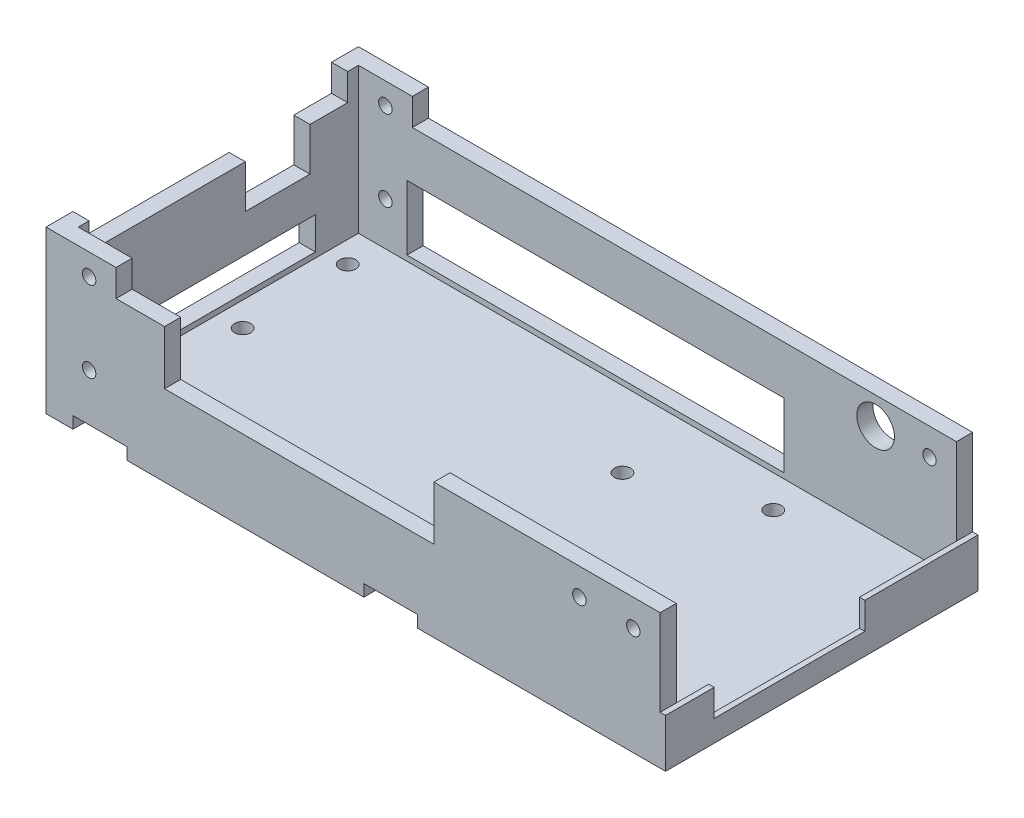
SolidWorks part; units mm, degrees
ref_plane "Front Plane" through (0, 0, 0) normal (0, 0, 1) x (1, 0, 0)
ref_plane "Top Plane" through (0, 0, 0) normal (0, 1, 0) x (1, 0, 0)
ref_plane "Right Plane" through (0, 0, 0) normal (1, 0, 0) x (0, 0, -1)
sketch "Sketch2" plane through (0, 0, 0) normal (0, 1, 0) x (1, 0, 0)
  line L1 (-76.4862, 30.6019) -> (37.5138, 30.6019)
  line L2 (-76.4862, 30.6019) -> (-76.4862, -27.3981)
  line L3 (-76.4862, -27.3981) -> (37.5138, -27.3981)
  line L4 (37.5138, 30.6019) -> (37.5138, -27.3981)
  dimension "D1" = 58
  dimension "D2" = 114
extrude "Boss-Extrude1" add sketch "Sketch2" along normal blind 3
sketch "Sketch3" plane through (0, 3, 0) normal (0, 1, 0) x (1, 0, 0)
  line L1 (37.5138, 30.6019) -> (-76.4862, 30.6019) construction
  line L2 (-76.4862, 30.6019) -> (-76.4862, -27.3981) construction
  circle A0 centre (-10.4862, 13.6019) radius 1.5
  circle A1 centre (-10.4862, -10.3981) radius 1.5
  circle A2 centre (-68.9862, 1.6019) radius 1.5
  dimension "D1" = 3
  dimension "D2" = 3
  dimension "D3" = 3
  dimension "D4" = 66
  dimension "D5" = 24
  dimension "D6" = 66
  dimension "D7" = 17
  dimension "D8" = 58.5
  dimension "D9" = 29
extrude "Cut-Extrude5" cut sketch "Sketch3" against normal through all
sketch "Sketch5" plane through (0, 0, 0) normal (0, -1, 0) x (-1, 0, 0)
  line L0 (-37.5138, 30.6019) -> (76.4862, 30.6019) construction
  circle A0 centre (23.4862, 16.8519) radius 3.025
  circle A2 centre (23.4862, -13.6481) radius 3.025
  circle A3 centre (53.9862, -13.6481) radius 3.025
  circle A4 centre (53.9862, 16.8519) radius 3.025
  circle A6 centre (10.4862, -10.3981) radius 1.5 construction
  circle A7 centre (10.4862, 13.6019) radius 1.5 construction
  dimension "D1" = 6.05
  dimension "D2" = 6.05
  dimension "D3" = 6.05
  dimension "D4" = 6.05
  dimension "D7" = 13
  dimension "D5" = 30.5
  dimension "D6" = 13.75
  dimension "D8" = 13
  dimension "D9" = 30.5
  dimension "D10" = 30.5
  dimension "D11" = 30.5
  dimension "D12" = 13.75
extrude "Cut-Extrude7" cut sketch "Sketch5" against normal blind 2.5
sketch "Sketch7" plane through (0, 3, 0) normal (0, 1, 0) x (1, 0, 0)
  line L0 (37.5138, 30.6019) -> (-76.4862, 30.6019) construction
  line L1 (-76.4862, 30.6019) -> (37.5138, 30.6019)
  line L2 (-76.4862, 30.6019) -> (-76.4862, 27.6019)
  line L3 (-76.4862, 27.6019) -> (37.5138, 27.6019)
  line L4 (37.5138, 30.6019) -> (37.5138, 27.6019)
  line L5 (-76.4862, -24.3981) -> (37.5138, -24.3981)
  line L6 (-76.4862, -24.3981) -> (-76.4862, -27.3981)
  line L7 (-76.4862, -27.3981) -> (37.5138, -27.3981)
  line L8 (37.5138, -24.3981) -> (37.5138, -27.3981)
  line L9 (-76.4862, 30.6019) -> (-76.4862, -27.3981) construction
  line L10 (-76.4862, 30.6019) -> (-76.4862, -27.3981) construction
  line L11 (-76.4862, -27.3981) -> (37.5138, -27.3981) construction
  line L12 (37.5138, -27.3981) -> (37.5138, 30.6019) construction
  line L14 (-76.4862, 27.6019) -> (-73.4862, 27.6019)
  line L15 (-76.4862, 27.6019) -> (-76.4862, -24.3981)
  line L16 (-76.4862, -24.3981) -> (-73.4862, -24.3981)
  line L17 (-73.4862, 27.6019) -> (-73.4862, -24.3981)
  point P16 (37.5138, 29.1019)
  dimension "D1" = 3
  dimension "D2" = 3
  dimension "D3" = 0
  dimension "D4" = 0
  dimension "D5" = 0
  dimension "D6" = 0
  dimension "D7" = 0
  dimension "D8" = 0
  dimension "D9" = 3
  dimension "D10" = 0
  dimension "D11" = 0
  dimension "D12" = 0
extrude "Boss-Extrude2" add sketch "Sketch7" along normal blind 22 contours L15 L14 L17 L16 | L2 L1 L4 L3 | L6 L5 L8 L7
sketch "Sketch8" plane through (0, 3, 0) normal (0, 1, 0) x (1, 0, 0)
  line L1 (-73.4862, 27.6019) -> (-73.4862, -24.3981) construction
  line L2 (-73.4862, -24.3981) -> (37.5138, -24.3981) construction
  circle A0 centre (-69.4862, 21.6019) radius 1.5
  circle A1 centre (-69.4862, -20.3981) radius 1.5
  circle A2 centre (9.5138, 21.6019) radius 1.5
  circle A3 centre (9.5138, -20.3981) radius 1.5
  dimension "D1" = 3
  dimension "D2" = 3
  dimension "D3" = 3
  dimension "D4" = 3
  dimension "D5" = 42
  dimension "D6" = 4
  dimension "D7" = 4
  dimension "D8" = 4
  dimension "D9" = 79
  dimension "D10" = 79
  dimension "D11" = 42
  dimension "D12" = 4
extrude "Cut-Extrude8" cut sketch "Sketch8" against normal up to next
sketch "Sketch9" plane through (0, 0, 27.3981) normal (0, 0, 1) x (1, 0, 0)
  line L0 (-76.4862, 25) -> (-76.4862, 0) construction
  line L1 (-54.4862, 25) -> (-4.4862, 25)
  line L2 (-54.4862, 25) -> (-54.4862, 15)
  line L3 (-54.4862, 15) -> (-4.4862, 15)
  line L4 (-4.4862, 25) -> (-4.4862, 15)
  line L5 (-76.4862, 25) -> (37.5138, 25) construction
  line L6 (-76.4862, 0) -> (37.5138, 0) construction
  dimension "D1" = 22
  dimension "D2" = 50
  dimension "D3" = 0
  dimension "D4" = 15
extrude "Cut-Extrude9" cut sketch "Sketch9" against normal up to next
sketch "Sketch10" plane through (-76.4862, 0, 0) normal (-1, 0, 0) x (0, 0, 1)
  line L0 (-30.6019, 0) -> (27.3981, 0) construction
  line L1 (-19.6019, 4) -> (12.3981, 4)
  line L2 (-19.6019, 4) -> (-19.6019, 10)
  line L3 (-19.6019, 10) -> (12.3981, 10)
  line L4 (12.3981, 4) -> (12.3981, 10)
  line L5 (-30.6019, 25) -> (-30.6019, 0) construction
  line L6 (27.3981, 25) -> (27.3981, 0) construction
  line L7 (-30.6019, 25) -> (27.3981, 25) construction
  line L8 (-18.6019, 25) -> (-6.6019, 25)
  line L9 (-18.6019, 25) -> (-18.6019, 17)
  line L10 (-18.6019, 17) -> (-6.6019, 17)
  line L11 (-6.6019, 25) -> (-6.6019, 17)
  dimension "D1" = 4
  dimension "D2" = 11
  dimension "D3" = 15
  dimension "D4" = 6
  dimension "D5" = 12
  dimension "D6" = 12
  dimension "D7" = 0
  dimension "D8" = 17
extrude "Cut-Extrude10" cut sketch "Sketch10" against normal up to next contours L9 L8 L11 L10 | L2 L1 L4 L3
sketch "Sketch11" plane through (0, 0, -30.6019) normal (0, 0, -1) x (-1, 0, 0)
  line L0 (76.4862, 25) -> (76.4862, 0) construction
  line L1 (64.4862, 4) -> (-5.5138, 4)
  line L2 (64.4862, 4) -> (64.4862, 16)
  line L3 (64.4862, 16) -> (-5.5138, 16)
  line L4 (-5.5138, 4) -> (-5.5138, 16)
  line L5 (-37.5138, 0) -> (76.4862, 0) construction
  dimension "D1" = 12
  dimension "D2" = 70
  dimension "D3" = 4
  dimension "D4" = 12
extrude "Cut-Extrude11" cut sketch "Sketch11" against normal up to next contours L2 L1 L4 L3
sketch "Sketch12" plane through (0, 0, 27.3981) normal (0, 0, 1) x (1, 0, 0)
  line L0 (37.5138, 25) -> (37.5138, 0) construction
  line L1 (-4.4862, 25) -> (37.5138, 25) construction
  line L2 (-76.4862, 25) -> (-76.4862, 0) construction
  line L3 (-76.4862, 0) -> (37.5138, 0) construction
  circle A0 centre (22.5138, 20) radius 1.25
  circle A1 centre (32.5138, 20) radius 1.25
  circle A3 centre (-68.4883, 11) radius 1.25
  dimension "D1" = 2.5
  dimension "D2" = 2.5
  dimension "D7" = 2.5
  dimension "D8" = 11
  dimension "D3" = 5
  dimension "D4" = 10
  dimension "D5" = 5
  dimension "D6" = 5
  dimension "D11" = 7.9979
extrude "Cut-Extrude12" cut sketch "Sketch12" against normal through all
sketch "Sketch13" plane through (0, 0, 27.3981) normal (0, 0, 1) x (1, 0, 0)
  line L0 (-76.4862, 25) -> (-54.4862, 25) construction
  line L1 (-76.4862, 30) -> (-63.4862, 30)
  line L2 (-76.4862, 30) -> (-76.4862, 25)
  line L3 (-76.4862, 25) -> (-63.4862, 25)
  line L4 (-63.4862, 30) -> (-63.4862, 25)
  line L6 (-76.4862, 25) -> (-76.4862, 0) construction
  dimension "D1" = 13
  dimension "D2" = 0
  dimension "D3" = 5
  dimension "D4" = 0
extrude "Boss-Extrude4" add sketch "Sketch13" against normal blind 3 contours L2 L1 L4 L3
sketch "Sketch14" plane through (0, 0, -30.6019) normal (0, 0, -1) x (-1, 0, 0)
  line L0 (63.4862, 30) -> (76.4862, 30)
  line L5 (63.4862, 30) -> (63.4862, 25)
  line L6 (63.4862, 25) -> (76.4862, 25)
  line L7 (76.4862, 30) -> (76.4862, 25)
  line L8 (76.4862, 25) -> (-37.5138, 25) construction
  line L9 (76.4862, 25) -> (76.4862, 0) construction
  dimension "D1" = 13
  dimension "D2" = 5
  dimension "D3" = 0
  dimension "D4" = 0
extrude "Boss-Extrude5" add sketch "Sketch14" against normal blind 3
sketch "Sketch15" plane through (0, 0, 27.3981) normal (0, 0, 1) x (1, 0, 0)
  line L0 (-76.4862, 30) -> (-63.4862, 30) construction
  line L1 (-76.4862, 30) -> (-76.4862, 0) construction
  circle A0 centre (-68.4862, 26) radius 1.25
  dimension "D1" = 2.5
  dimension "D2" = 4
  dimension "D3" = 8
extrude "Cut-Extrude13" cut sketch "Sketch15" against normal through all contours A0
sketch "Sketch16" plane through (-76.4862, 0, 0) normal (-1, 0, 0) x (0, 0, 1)
  line L0 (-27.6019, 25) -> (-18.6019, 25) construction
  line L1 (-27.6019, 30) -> (-25.6019, 30)
  line L2 (-27.6019, 30) -> (-27.6019, 25)
  line L3 (-27.6019, 25) -> (-25.6019, 25)
  line L4 (-25.6019, 30) -> (-25.6019, 25)
  line L5 (22.3981, 30) -> (24.3981, 30)
  line L6 (22.3981, 30) -> (22.3981, 25)
  line L7 (22.3981, 25) -> (24.3981, 25)
  line L8 (24.3981, 30) -> (24.3981, 25)
  line L9 (-27.6019, 30) -> (-30.6019, 30) construction
  line L10 (-27.6019, 25) -> (-27.6019, 30) construction
  line L11 (-6.6019, 25) -> (24.3981, 25) construction
  line L12 (24.3981, 30) -> (24.3981, 25) construction
  line L13 (24.3981, 30) -> (27.3981, 30) construction
  line M18 (24.3981, 30) -> (24.3981, 25)
  line M19 (24.3981, 25) -> (-6.6019, 25)
  dimension "D1" = 2
  dimension "D2" = 0
  dimension "D3" = 0
  dimension "D4" = 0
  dimension "D5" = 2
  dimension "D6" = 0
  dimension "D7" = 0
  dimension "D8" = 0
extrude "Boss-Extrude6" add sketch "Sketch16" against normal blind 3 contours L5 L6 M19 M18 | L2 L1 L4 L3
sketch "Sketch17" plane through (0, 0, -27.6019) normal (0, 0, 1) x (1, 0, 0)
  line L0 (-73.4862, 3) -> (37.5138, 3) construction
  line L1 (37.5138, 25) -> (37.5138, 3) construction
  circle A0 centre (22.5138, 20) radius 3.5
  dimension "D1" = 7
  dimension "D2" = 17
  dimension "D3" = 15
extrude "Cut-Extrude14" cut sketch "Sketch17" against normal up to next
sketch "Sketch19" plane through (0, 0, 0) normal (0, -1, 0) x (1, 0, 0)
  line L0 (37.5138, 27.3981) -> (37.5138, -30.6019) construction
  line L1 (37.5138, 27.3981) -> (38.5138, 27.3981)
  line L2 (37.5138, 27.3981) -> (37.5138, -30.6019)
  line L3 (37.5138, -30.6019) -> (38.5138, -30.6019)
  line L4 (38.5138, 27.3981) -> (38.5138, -30.6019)
  line L5 (37.5138, -30.6019) -> (-76.4862, -30.6019) construction
  line L6 (-76.4862, 27.3981) -> (37.5138, 27.3981) construction
  dimension "D1" = 1
  dimension "D2" = 0
  dimension "D3" = 0
  dimension "D4" = 0
extrude "Boss-Extrude7" add sketch "Sketch19" against normal blind 9 contours L2 L1 L4 L3
sketch "Sketch20" plane through (38.5138, 0, 0) normal (1, 0, 0) x (0, 0, -1)
  line L0 (-27.3981, 9) -> (-27.3981, 0) construction
  line L1 (-18.3981, 9) -> (9.6019, 9)
  line L2 (-18.3981, 9) -> (-18.3981, 4)
  line L3 (-18.3981, 4) -> (9.6019, 4)
  line L4 (9.6019, 9) -> (9.6019, 4)
  line L5 (-27.3981, 0) -> (30.6019, 0) construction
  line L6 (-27.3981, 9) -> (30.6019, 9) construction
  dimension "D1" = 28
  dimension "D2" = 9
  dimension "D3" = 4
  dimension "D4" = 0
extrude "Cut-Extrude15" cut sketch "Sketch20" against normal up to next contours L2 L1 L4 L3
sketch "Sketch21" plane through (0, 0, 0) normal (0, -1, 0) x (-1, 0, 0)
  line L0 (76.4862, -27.3981) -> (-38.5138, -27.3981) construction
  line L1 (71.4862, -27.3981) -> (61.4862, -27.3981)
  line L2 (71.4862, -27.3981) -> (71.4862, -24.8981)
  line L3 (71.4862, -24.8981) -> (61.4862, -24.8981)
  line L4 (61.4862, -27.3981) -> (61.4862, -24.8981)
  line L5 (71.4862, 28.1019) -> (61.4862, 28.1019)
  line L6 (71.4862, 28.1019) -> (71.4862, 30.6019)
  line L7 (71.4862, 30.6019) -> (61.4862, 30.6019)
  line L8 (61.4862, 28.1019) -> (61.4862, 30.6019)
  line L9 (17.4862, -27.3981) -> (7.4862, -27.3981)
  line L10 (17.4862, -27.3981) -> (17.4862, -24.8981)
  line L11 (17.4862, -24.8981) -> (7.4862, -24.8981)
  line L12 (7.4862, -27.3981) -> (7.4862, -24.8981)
  line L13 (17.4862, 28.1019) -> (7.4862, 28.1019)
  line L14 (17.4862, 28.1019) -> (17.4862, 30.6019)
  line L15 (17.4862, 30.6019) -> (7.4862, 30.6019)
  line L16 (7.4862, 28.1019) -> (7.4862, 30.6019)
  line L17 (-38.5138, 30.6019) -> (76.4862, 30.6019) construction
  line L18 (76.4862, 30.6019) -> (76.4862, -27.3981) construction
  point P22 (17.4862, -26.1481)
  line M29 (76.4862, 30.6019) -> (-38.5138, 30.6019)
  line M31 (-38.5138, -27.3981) -> (76.4862, -27.3981)
  dimension "D1" = 10
  dimension "D2" = 10
  dimension "D3" = 10
  dimension "D4" = 10
  dimension "D5" = 0
  dimension "D6" = 0
  dimension "D7" = 0
  dimension "D8" = 0
  dimension "D9" = 5
  dimension "D10" = 2.5
  dimension "D11" = 59
  dimension "D12" = 2.5
  dimension "D13" = 2.5
  dimension "D14" = 2.5
  dimension "D15" = 5
  dimension "D16" = 59
extrude "Cut-Extrude16" cut sketch "Sketch21" against normal blind 2.2 contours L4 L2 L3 M31 | L12 L10 L11 M31 | L16 L13 L14 M29 | L6 L5 L8 L7
